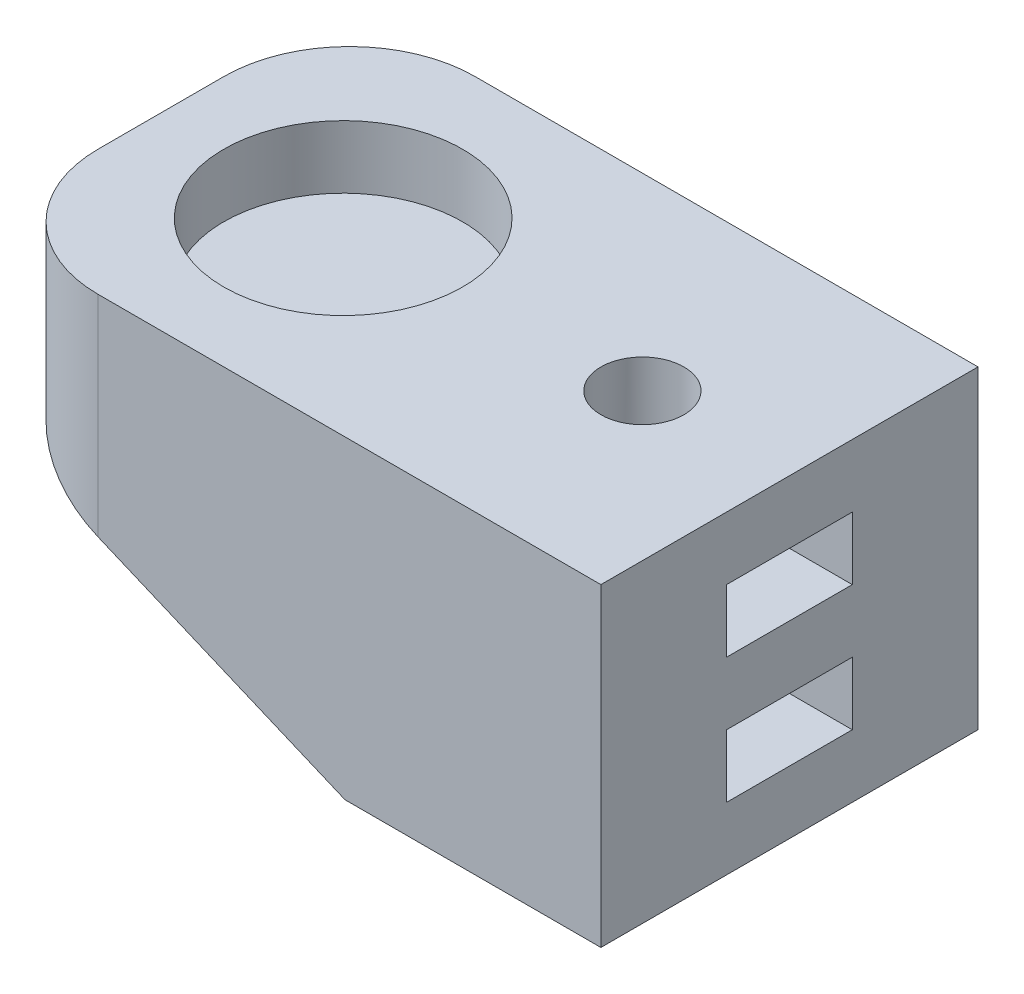
SolidWorks part; units mm, degrees
ref_plane "Plan de face" through (0, 0, 0) normal (0, 0, 1) x (1, 0, 0)
ref_plane "Plan de dessus" through (0, 0, 0) normal (0, 1, 0) x (1, 0, 0)
ref_plane "Plan de droite" through (0, 0, 0) normal (1, 0, 0) x (0, 0, -1)
sketch "Esquisse1" plane through (0, 0, 0) normal (0, 1, 0) x (1, 0, 0)
  line L1 (-60.542, 46.94) -> (-10.542, 46.94)
  line L2 (-60.542, 46.94) -> (-60.542, 16.94)
  line L3 (-60.542, 16.94) -> (-10.542, 16.94)
  line L4 (-10.542, 46.94) -> (-10.542, 16.94)
  dimension "D1" = 50
  dimension "D2" = 30
extrude "Boss.-Extru.1" add sketch "Esquisse1" along normal blind 25
sketch "Esquisse2" plane through (0, 25, 0) normal (0, 1, 0) x (1, 0, 0)
  line L0 (-60.542, 31.94) -> (-10.542, 31.94) construction
  line L1 (-60.542, 46.94) -> (-60.542, 16.94) construction
  line L2 (-10.542, 16.94) -> (-10.542, 46.94) construction
  circle A0 centre (-46.042, 31.94) radius 9.5
  circle A1 centre (-16.0811, 31.94) radius 3.3
  point P10 (-46.042, 31.94)
  point P11 (-52.8732, 67.655)
  point P12 (-46.042, 31.94)
  dimension "D1" = 19
  dimension "D3" = 6.6
  dimension "D2" = 14.5
  dimension "D4" = 0
  dimension "D5" = 0
extrude "Enlèv. mat.-Extru.1" cut sketch "Esquisse2" against normal blind 5 contours A0
sketch "Esquisse5" plane through (0, 25, 0) normal (0, 1, 0) x (1, 0, 0)
  line L0 (-60.542, 31.94) -> (-10.542, 31.94) construction
  line L1 (-60.542, 46.94) -> (-60.542, 16.94) construction
  line L2 (-10.542, 16.94) -> (-10.542, 46.94) construction
  circle A0 centre (-22.2401, 31.94) radius 3.3
  point P8 (-22.2401, 31.94)
  dimension "D1" = 6.6
  dimension "D2" = 0
extrude "Enlèv. mat.-Extru.2" cut sketch "Esquisse5" against normal blind 30
sketch "Esquisse6" plane through (0, 25, 0) normal (0, 1, 0) x (1, 0, 0)
  line L0 (-10.542, 31.94) -> (-30.9017, 31.94) construction
  line L1 (-10.542, 16.94) -> (-10.542, 46.94) construction
  line L2 (-30.9017, 31.94) -> (-30.9017, 46.94) construction
  line L3 (-10.542, 46.94) -> (-60.542, 46.94) construction
sketch "Esquisse7" plane through (0, 0, -46.94) normal (0, 0, -1) x (-1, 0, 0)
  line L0 (30.9017, 25) -> (30.9017, 0) construction
  line L1 (10.542, 25) -> (30.9017, 25) construction
  line L2 (10.542, 25) -> (60.542, 25) construction
  line L3 (10.542, 0) -> (60.542, 0) construction
  line L4 (30.9017, 0) -> (60.542, 12.5) construction
  line L5 (60.542, 25) -> (60.542, 0) construction
  line L6 (30.9017, 0) -> (60.542, 0) construction
  line L7 (60.542, 0) -> (60.542, 12.5) construction
  line L8 (30.9017, 0) -> (60.542, 12.5)
  line L9 (60.542, 12.5) -> (60.542, 0)
  line L10 (60.542, 0) -> (30.9017, 0)
extrude "Enlèv. mat.-Extru.3" cut sketch "Esquisse7" against normal blind 30
fillet "Congé1" radius 10 2 edges at (-60.542, 18.75, -16.94) (-60.542, 18.75, -46.94)
sketch "Esquisse8" plane through (0, 0, 0) normal (0, -1, 0) x (1, 0, 0)
  line L0 (-19.3534, -36.94) -> (-10.542, -36.94)
  line L1 (-16.4666, -31.94) -> (-19.3534, -26.94)
  line L2 (-19.3534, -26.94) -> (-25.1269, -26.94)
  line L3 (-25.1269, -26.94) -> (-28.0136, -31.94)
  line L4 (-28.0136, -31.94) -> (-25.1269, -36.94)
  line L5 (-25.1269, -36.94) -> (-19.3534, -36.94)
  line L6 (-19.3534, -36.94) -> (-16.4666, -31.94)
  line L7 (-10.542, -16.94) -> (-10.542, -46.94) construction
  line L8 (-19.3534, -26.94) -> (-10.542, -26.94)
  circle A0 centre (-22.2401, -31.94) radius 5 construction
  circle M7 centre (-22.2401, -31.94) radius 3.3
  line M11 (-10.542, -46.94) -> (-10.542, -16.94)
  dimension "D1" = 10
extrude "Enlèv. mat.-Extru.4" cut sketch "Esquisse8" against normal blind 5 from offset 5 contours L5 L6 L1 L2 L3 L4 M7 | L8 L1 L6 L0 M11 offset against normal yes
pattern_linear "Répétition linéaire1" count 2 spacing 10 along (0, 1, 0) of "Enlèv. mat.-Extru.4"
